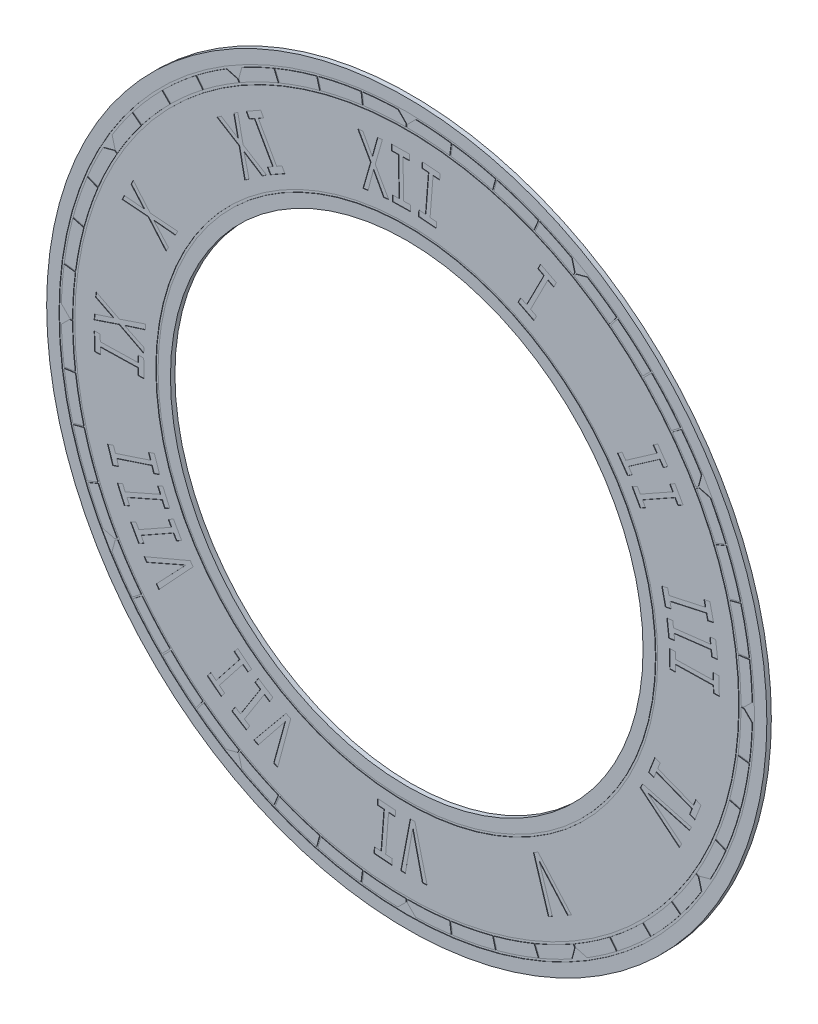
SolidWorks part; units mm, degrees
ref_plane "Front Plane" through (0, 0, 0) normal (0, 0, 1) x (1, 0, 0)
ref_plane "Top Plane" through (0, 0, 0) normal (0, 1, 0) x (1, 0, 0)
ref_plane "Right Plane" through (0, 0, 0) normal (1, 0, 0) x (0, 0, -1)
sketch "Sketch1" plane through (0, 0, 0) normal (0, 0, 1) x (1, 0, 0)
  circle A0 centre (0, 0) radius 52.5 construction
  circle A1 centre (0, 0) radius 80 construction
  circle A2 centre (0, 0) radius 52.5
  circle A3 centre (0, 0) radius 80
extrude "Boss-Extrude1" add sketch "Sketch1" along normal blind 1
sketch "Sketch2" plane through (0, 0, 1) normal (0, 0, 1) x (1, 0, 0)
  circle A0 centre (0, 0) radius 55.5
  circle A1 centre (0, 0) radius 77
  circle A2 centre (0, 0) radius 74
  circle A3 centre (0, 0) radius 80 construction
  circle A4 centre (0, 0) radius 52.5 construction
  dimension "D1" = 3
  dimension "D2" = 3
  dimension "D3" = 3
extrude "Cut-Extrude-Thin2" cut sketch "Sketch2" against normal blind 0.1 thin contours A1 A2 | A0 thin type mid plane wall 0.5
sketch "Sketch5" plane through (0, 0, 1) normal (0, 0, 1) x (1, 0, 0)
  line L0 (0, 74) -> (0, 77)
  circle A2 centre (0, 0) radius 77 construction
  circle A3 centre (0, 0) radius 74 construction
extrude "Cut-Extrude-Thin5" cut sketch "Sketch5" against normal blind 0.1 and the other way through all thin thin type mid plane wall 0.3
pattern_circular "CirPattern2" count 48 over 360 about axis through (0, 0, 0) along (0, 0, 1) of "Cut-Extrude-Thin5"
sketch "Sketch3" plane through (0, 0, 1) normal (0, 0, 1) x (1, 0, 0)
  line L0 (0, 0) -> (0, 80) construction
  line L1 (-2, 76.75) -> (2, 76.75)
  line L2 (-2, 76.75) -> (0, 74.75)
  line L3 (0, 74.75) -> (2, 76.75)
  circle A0 centre (0, 0) radius 80 construction
  circle A1 centre (0, 0) radius 76.75 construction
  point P10 (0, 76.75)
  dimension "D1" = 4
  dimension "D2" = 2
extrude "Cut-Extrude1" cut sketch "Sketch3" against normal blind 0.1
pattern_circular "CirPattern1" count 12 over 360 about axis through (0, 0, 0) along (0, 0, 1) of "Cut-Extrude1"
sketch "Sketch6" plane through (0, 0, 1) normal (0, 0, 1) x (1, 0, 0)
  line L0 (-10.1584, 57.6113) -> (0, 0) construction
  arc A2 (-10.1584, 57.6113) -> (-15.1409, 56.5067) centre (0, 0) cw construction
  circle A3 centre (0, 0) radius 52.5 construction
  text T0 "XII   I    II  III   IV     V    VI   VII  VIII  IX   X    XI  " font "Monospac821 BT" height 11
  dimension "D1" = 6
  dimension "D2" = 355
  dimension "D3" = 10
extrude "Cut-Extrude5" cut sketch "Sketch6" against normal blind 0.1
